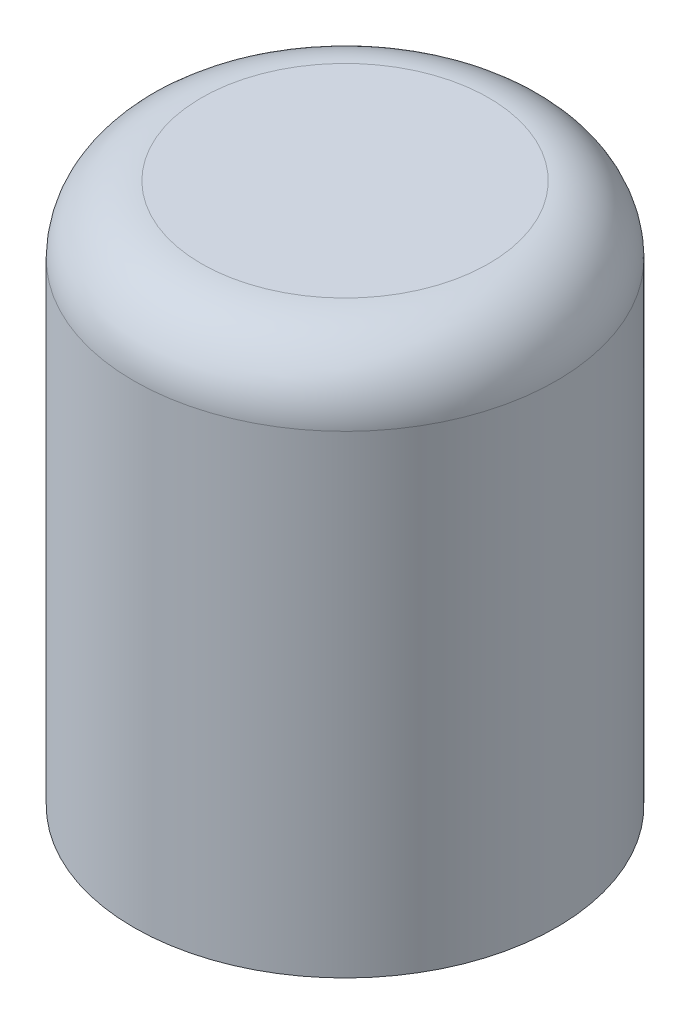
SolidWorks part; units mm, degrees
ref_plane "Front Plane" through (0, 0, 0) normal (0, 0, 1) x (1, 0, 0)
ref_plane "Top Plane" through (0, 0, 0) normal (0, 1, 0) x (1, 0, 0)
ref_plane "Right Plane" through (0, 0, 0) normal (1, 0, 0) x (0, 0, -1)
sketch "Sketch1" plane through (0, 0, 0) normal (0, 1, 0) x (1, 0, 0)
  circle A0 centre (0, 0) radius 3.125
  dimension "D1" = 6.25
extrude "Boss-Extrude1" add sketch "Sketch1" along normal blind 8
sketch "Sketch2" plane through (0, 0, 0) normal (0, -1, 0) x (1, 0, 0)
  line L1 (-1.125, -1.625) -> (1.125, -1.625)
  line L2 (-1.125, -1.625) -> (-1.125, 1.625)
  line L3 (-1.125, 1.625) -> (1.125, 1.625)
  line L4 (1.125, -1.625) -> (1.125, 1.625)
  line L5 (-1.125, -1.625) -> (1.125, 1.625) construction
  line L6 (-1.125, 1.625) -> (1.125, -1.625) construction
  point P0 (0, 0)
  dimension "D1" = 3.25
  dimension "D2" = 2.25
extrude "Cut-Extrude1" cut sketch "Sketch2" against normal blind 3
fillet "Fillet1" radius 1 1 edges at (0, 8, 3.125)
